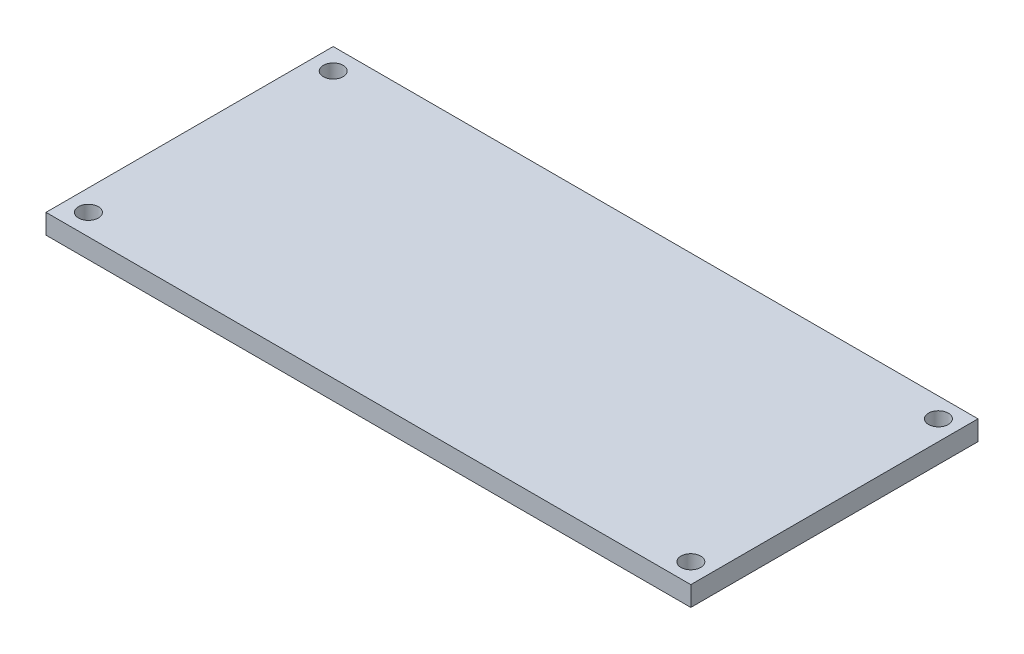
SolidWorks part; units mm, degrees
ref_plane "Front" through (0, 0, 0) normal (0, 0, 1) x (1, 0, 0)
ref_plane "Top" through (0, 0, 0) normal (0, 1, 0) x (1, 0, 0)
ref_plane "Right" through (0, 0, 0) normal (1, 0, 0) x (0, 0, -1)
sketch "Sketch1" plane through (0, 0, 0) normal (0, 1, 0) x (1, 0, 0)
  line L1 (-22.6608, 12.1624) -> (22.9392, 12.1624)
  line L2 (-22.6608, 12.1624) -> (-22.6608, -8.1476)
  line L3 (-22.6608, -8.1476) -> (22.9392, -8.1476)
  line L4 (22.9392, 12.1624) -> (22.9392, -8.1476)
  line L5 (-22.6608, 12.1624) -> (22.9392, -8.1476) construction
  line L6 (-22.6608, -8.1476) -> (22.9392, 12.1624) construction
  circle A0 centre (-21.1608, 10.6624) radius 0.7
  circle A1 centre (-21.1608, -6.6476) radius 0.7
  circle A2 centre (21.5392, 10.7624) radius 0.7
  circle A3 centre (21.5392, -6.7476) radius 0.7
  point P4 (0.1392, 2.0074)
  dimension "D3" = 1.4
  dimension "D4" = 1.4
  dimension "D5" = 1.4
  dimension "D6" = 1.4
  dimension "D1" = 45.6
  dimension "D2" = 20.31
  dimension "D7" = 1.5
  dimension "D8" = 1.5
  dimension "D9" = 1.5
  dimension "D10" = 1.5
  dimension "D11" = 1.4
  dimension "D12" = 1.4
  dimension "D13" = 1.4
  dimension "D14" = 1.4
extrude "Boss-Extrude1" add sketch "Sketch1" along normal blind 1.4
